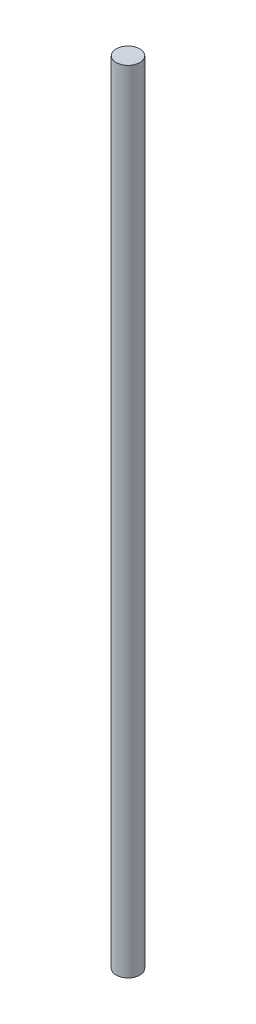
SolidWorks part; units mm, degrees
ref_plane "Alzado" through (0, 0, 0) normal (0, 0, 1) x (1, 0, 0)
ref_plane "Planta" through (0, 0, 0) normal (0, 1, 0) x (1, 0, 0)
ref_plane "Vista lateral" through (0, 0, 0) normal (1, 0, 0) x (0, 0, -1)
sketch "Croquis1" plane through (0, 0, 0) normal (0, 1, 0) x (1, 0, 0)
  circle A0 centre (0, 0) radius 3
  dimension "D1" = 6
extrude "Saliente-Extruir1" add sketch "Croquis1" along normal blind 200
